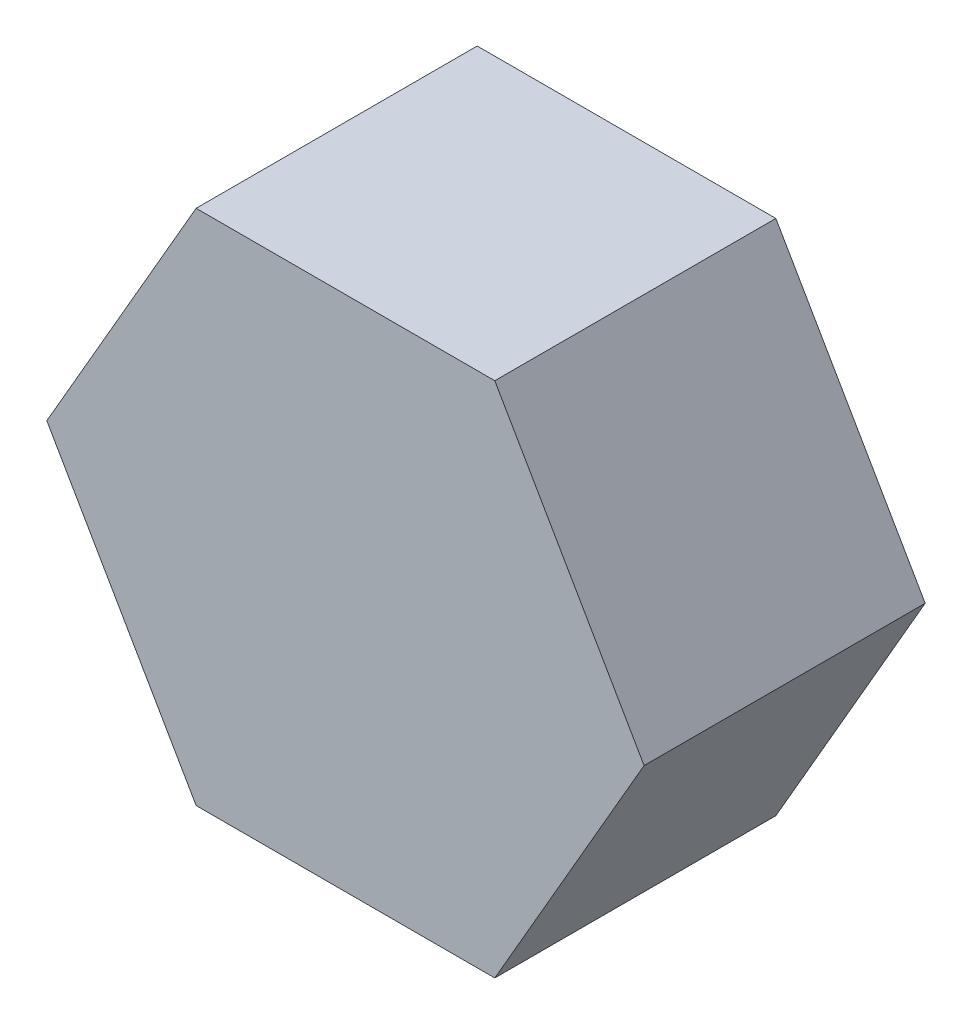
SolidWorks part; units mm, degrees
ref_plane "Front Plane" through (0, 0, 0) normal (0, 0, 1) x (1, 0, 0)
ref_plane "Top Plane" through (0, 0, 0) normal (0, 1, 0) x (1, 0, 0)
ref_plane "Right Plane" through (0, 0, 0) normal (1, 0, 0) x (0, 0, -1)
sketch "Sketch1" plane through (0, 0, 0) normal (0, 0, 1) x (1, 0, 0)
  line L0 (-20.8671, 25.219) -> (-12.3671, 25.219)
  line L1 (-12.3671, 25.219) -> (-8.1171, 17.8578)
  line L2 (-8.1171, 17.8578) -> (-12.3671, 10.4966)
  line L3 (-12.3671, 10.4966) -> (-20.8671, 10.4966)
  line L4 (-20.8671, 10.4966) -> (-25.1171, 17.8578)
  line L5 (-25.1171, 17.8578) -> (-20.8671, 25.219)
  dimension "D1" = 120
  dimension "D2" = 120
  dimension "D3" = 120
  dimension "D4" = 120
  dimension "D5" = 120
  dimension "D6" = 120
  dimension "D7" = 17
extrude "Boss-Extrude1" add sketch "Sketch1" along normal blind 8
